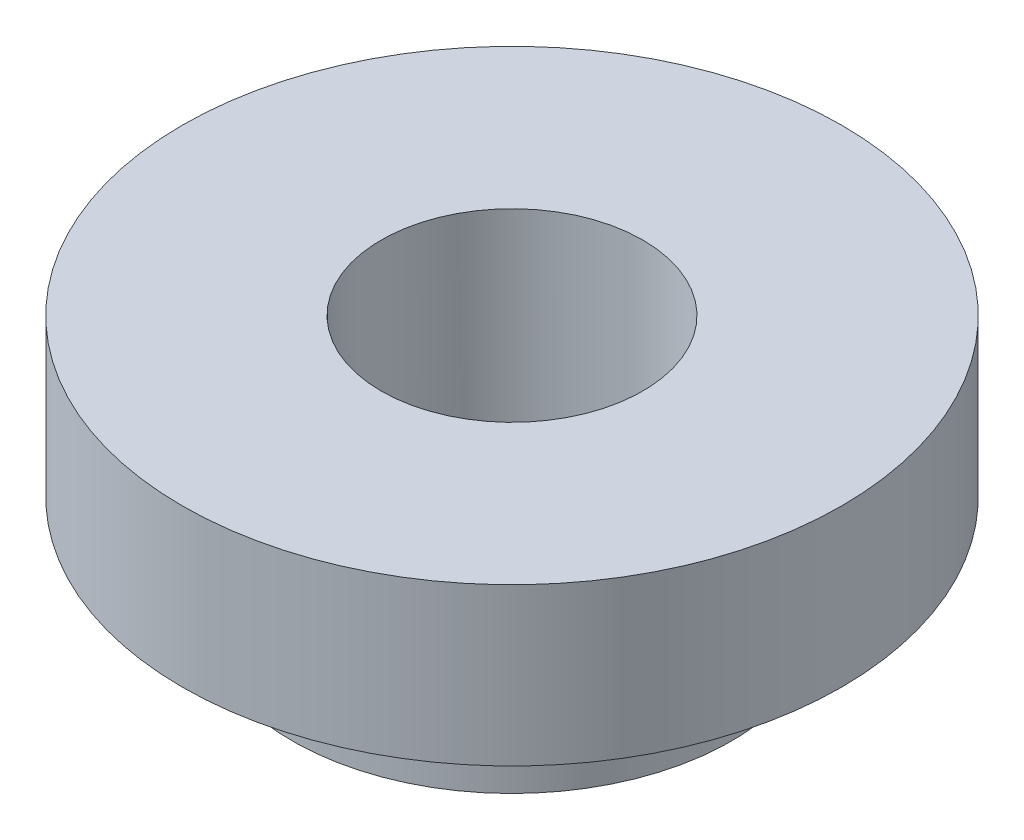
SolidWorks part; units mm, degrees
material "acero"
ref_plane "Alzado" through (0, 0, 0) normal (0, 0, 1) x (1, 0, 0)
ref_plane "Planta" through (0, 0, 0) normal (0, 1, 0) x (1, 0, 0)
ref_plane "Vista lateral" through (0, 0, 0) normal (1, 0, 0) x (0, 0, -1)
sketch "Croquis1" plane through (0, 0, 0) normal (0, 0, 1) x (1, 0, 0)
  line L0 (0, 0) -> (3.15, 0)
  line L1 (3.15, 0) -> (3.15, -1.5)
  line L2 (3.15, -1.5) -> (2.1, -1.5)
  line L3 (2.1, -1.5) -> (2.1, -2.47)
  line L4 (2.1, -2.47) -> (0, -2.47)
  line L5 (0, 0) -> (0, -2.47)
  dimension "D1" = 3.15
  dimension "D2" = 1.5
  dimension "D3" = 0.97
  dimension "D4" = 2.1
revolve "Revolución1" add sketch "Croquis1" angle 360 about L5
hole_wizard "Taladro roscado M31" positions "Croquis3" profile "Croquis2" tap size "M3" standard "Din"
sketch "Croquis3" plane through (0, 0, 0) normal (0, 1, 0) x (1, 0, 0)
  point P0 (0, 0)
sketch "Croquis2" plane through (0, 0, 0) normal (1, 0, 0) x (0, 0, 1)
  line L0 (0, 0) -> (0, 10.7511)
  line L1 (0, 10.7511) -> (1.25, 10)
  line L2 (1.25, 10) -> (1.25, 0)
  line L5 (1.25, 0) -> (0, 0)
  line L10 (0, 10.7511) -> (-1.25, 10) construction
  line L11 (0, -6.35) -> (0, 107.95) construction
  dimension "Diámetro de perforador para roscar" = 2.5
  dimension "Profundidad de perforador para roscar" = 10
  dimension "Ángulo de perforador" = 118
cosmetic thread "Rosca de taladro1" parameters "D1"=2.47, "D2"=3
